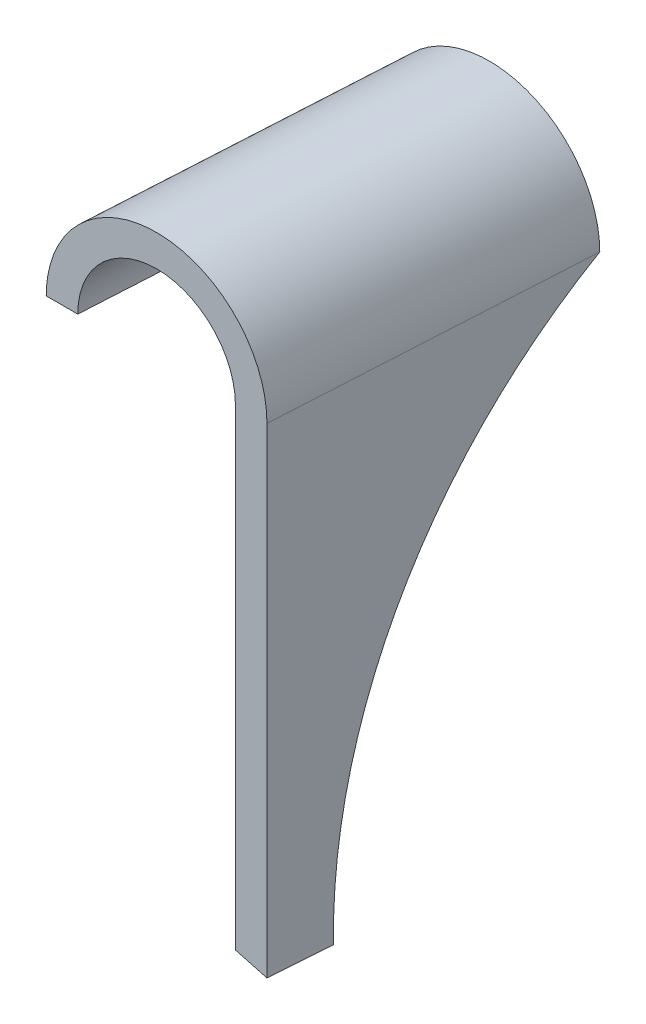
SolidWorks part; units mm, degrees
ref_plane "Front Plane" through (0, 0, 0) normal (0, 0, 1) x (1, 0, 0)
ref_plane "Top Plane" through (0, 0, 0) normal (0, 1, 0) x (1, 0, 0)
ref_plane "Right Plane" through (0, 0, 0) normal (1, 0, 0) x (0, 0, -1)
sketch "Sketch1" plane through (0, 0, 0) normal (0, 0, 1) x (1, 0, 0)
  line L0 (0, -23.8125) -> (0, 23.8125)
  line L1 (-15, -38.8125) -> (-120, -38.8125)
  line L2 (-15, -38.8125) -> (-119.7785, -10.7372)
  line L3 (-15, 38.8125) -> (-119.7785, 66.8878)
  line L4 (-119.7785, -10.7372) -> (-119.7785, 66.8878)
  arc A0 (0, 23.8125) -> (-15, 38.8125) centre (-15, 23.8125) ccw
  circle A1 centre (-15, 23.8125) radius 3.2639
  circle A2 centre (-15, -23.8125) radius 3.2639
  arc A3 (0, -23.8125) -> (-15, -38.8125) centre (-15, -23.8125) cw
  point P8 (-111.1285, 58.222)
  dimension "D2" = 30
  dimension "D3" = 6.5278
  dimension "D7" = 6.5278
  dimension "D1" = 47.625
  dimension "D4" = 105
  dimension "D5" = 15
  dimension "D6" = 108.4747
extrude "Boss-Extrude1" add sketch "Sketch1" along normal blind 10 contours A3 L0 A0 L3 L4 L2 A1 A2
sketch "Sketch2" plane through (0, 0, 10) normal (0, 0, 1) x (1, 0, 0)
  line L0 (-109.7785, 64.2083) -> (-109.7785, 103.7647)
  line L1 (-15, 38.8125) -> (-119.7785, 66.8878) construction
  line L2 (-109.7785, 103.7647) -> (-165.743, 103.7647)
  line L3 (-165.743, 103.7647) -> (-165.743, 64.2083)
  line L4 (-165.743, 64.2083) -> (-109.7785, 64.2083)
  dimension "D1" = 10
extrude "Boss-Extrude2" add sketch "Sketch2" against normal blind 50
ref_plane "Plane1" through (-0.9592, 0, 16.7887) normal (-0.057, 0, 0.9984) x (0, 1, 0)
sketch "Sketch4" plane through (-0.9592, 0, 16.7887) normal (-0.057, 0, 0.9984) x (0, 1, 0)
  line L1 (64.2083, 144.013) -> (64.2083, 119.013)
  line L3 (64.2083, 149.013) -> (64.2083, 176.7001)
  line L4 (64.2083, 164.9027) -> (64.2083, 119.013) construction
  line L5 (64.2083, 176.7001) -> (111.9846, 176.7001)
  line L6 (111.9846, 176.7001) -> (111.9846, 106.9013)
  line L7 (111.9846, 106.9013) -> (64.2083, 106.9013)
  line L8 (64.2083, 106.9013) -> (64.2083, 114.013)
  arc A0 (64.2083, 119.013) -> (64.2083, 144.013) centre (64.2083, 131.513) ccw
  arc A1 (64.2083, 114.013) -> (64.2083, 149.013) centre (64.2083, 131.513) ccw
  dimension "D1" = 25
  dimension "D3" = 35
extrude "Cut-Extrude1" cut sketch "Sketch4" against normal through all and the other way through all contours A1 L8 L7 L6 L5 L3 | L1 A0
sketch "Sketch7" plane through (0, 64.2083, 0) normal (0, 1, 0) x (1, 0, 0)
  line L0 (-119.7785, 0) -> (-119.2071, 0)
  line L1 (-119.2071, 0) -> (-119.7785, -10)
  line L2 (-119.7785, -10) -> (-119.7785, 0)
  point P4 (-119.7785, -0.0106)
extrude "Cut-Extrude3" cut sketch "Sketch7" against normal through all
sketch "Sketch8" plane through (0, 64.2083, 0) normal (0, -1, 0) x (1, 0, 0)
  line L0 (-119.2071, 0) -> (-116.9218, -40)
  line L1 (-116.9218, -40) -> (-111.9136, -40)
  line L2 (-111.9136, -40) -> (-114.199, 0)
  line L3 (-114.199, 0) -> (-119.2071, 0)
extrude "Boss-Extrude3" add sketch "Sketch8" along normal up to surface (77.0529 mm away)
sketch "Sketch10" plane through (-113.8274, 0, -6.5035) normal (0.9984, 0, 0.057) x (0.057, 0, -0.9984)
  circle A0 centre (83.4725, -10.6773) radius 90
extrude "Cut-Extrude4" cut sketch "Sketch10" against normal blind 50
fillet "Fillet4" [suppressed] radius 5
sketch "Sketch13" plane through (-0.9592, 0, 16.7887) normal (-0.057, 0, 0.9984) x (0, 1, 0)
  line L0 (64.2083, 114.013) -> (-14.4067, 114.013)
  line L1 (-14.4067, 114.013) -> (-68.1387, -11.1614)
  line L2 (-68.1387, -11.1614) -> (108.5671, -47.6245)
  line L3 (108.5671, -47.6245) -> (64.2083, 114.013)
extrude "Cut-Extrude5" cut sketch "Sketch13" against normal blind 50
